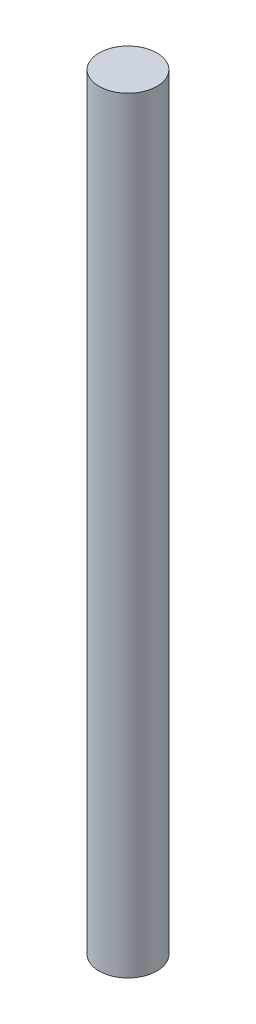
SolidWorks part; units mm, degrees
material "Chrome Stainless Steel"
ref_plane "Front Plane" through (0, 0, 0) normal (0, 0, 1) x (1, 0, 0)
ref_plane "Top Plane" through (0, 0, 0) normal (0, 1, 0) x (1, 0, 0)
ref_plane "Right Plane" through (0, 0, 0) normal (1, 0, 0) x (0, 0, -1)
sketch "Sketch1" plane through (0, 0, 0) normal (0, 1, 0) x (1, 0, 0)
  circle A0 centre (0, 0) radius 3.175
  dimension "D1" = 6.35
extrude "Boss-Extrude1" add sketch "Sketch1" along normal blind 84.074
